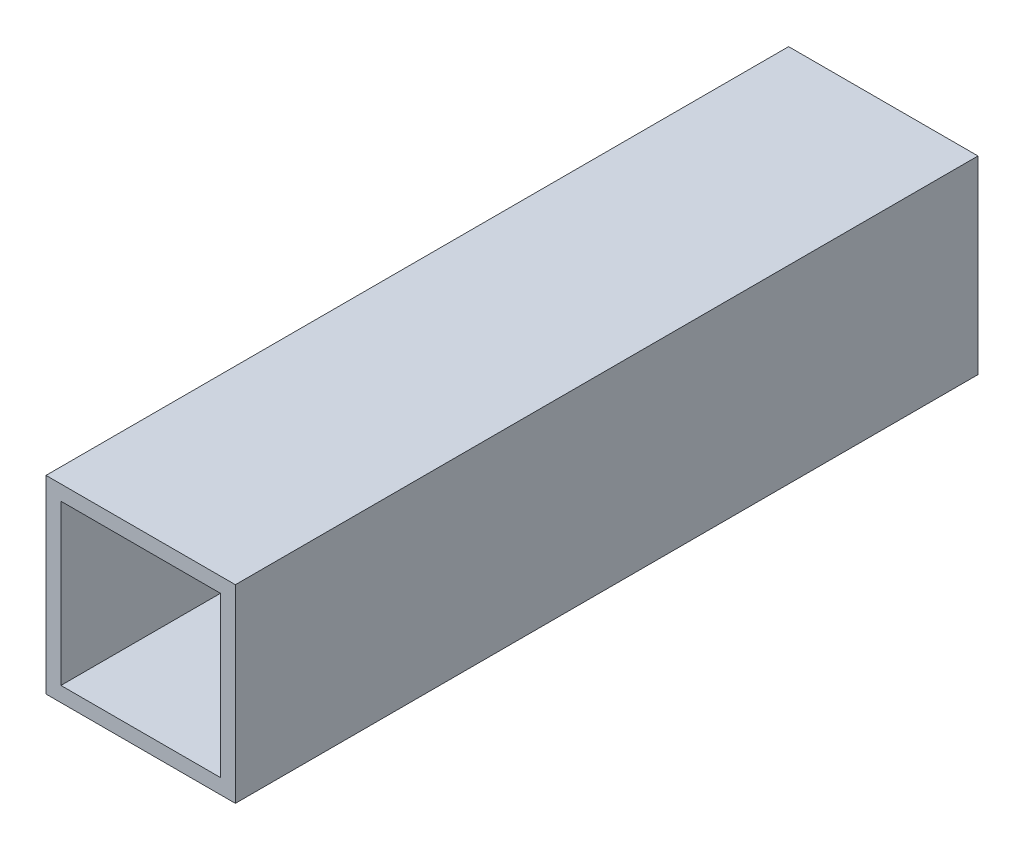
SolidWorks part; units mm, degrees
ref_plane "Front Plane" through (0, 0, 0) normal (0, 0, 1) x (1, 0, 0)
ref_plane "Top Plane" through (0, 0, 0) normal (0, 1, 0) x (1, 0, 0)
ref_plane "Right Plane" through (0, 0, 0) normal (1, 0, 0) x (0, 0, -1)
sketch "Sketch1" plane through (0, 0, 0) normal (0, 0, 1) x (1, 0, 0)
  line L0 (-10.7, 10.7) -> (10.7, 10.7)
  line L1 (-12.7, -12.7) -> (12.7, -12.7)
  line L2 (-12.7, -12.7) -> (-12.7, 12.7)
  line L3 (-12.7, 12.7) -> (12.7, 12.7)
  line L4 (12.7, -12.7) -> (12.7, 12.7)
  line L5 (-12.7, -12.7) -> (12.7, 12.7) construction
  line L6 (-12.7, 12.7) -> (12.7, -12.7) construction
  line L7 (10.7, -10.7) -> (10.7, 10.7)
  line L8 (-10.7, -10.7) -> (10.7, -10.7)
  line L9 (-10.7, -10.7) -> (-10.7, 10.7)
  point P0 (0, 0)
  dimension "D1" = 25.4
  dimension "D2" = 2
extrude "Boss-Extrude1" add sketch "Sketch1" along normal blind 99.6
